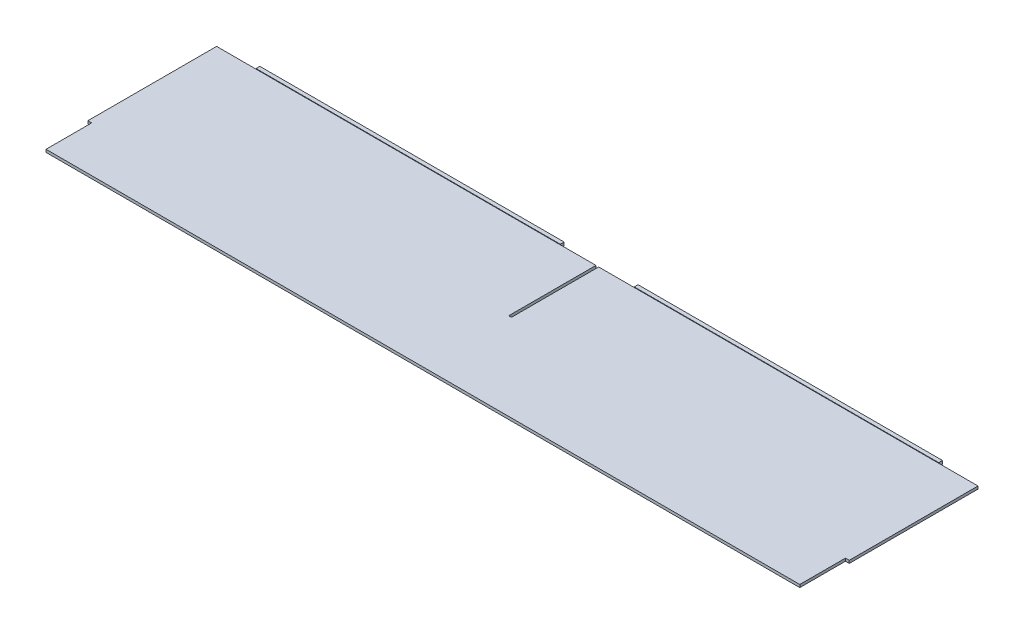
SolidWorks part; units mm, degrees
material "6061-T6 (SS)"
ref_plane "X-Y Datum" through (0, 0, 0) normal (0, 0, 1) x (1, 0, 0)
ref_plane "X-Z Datum" through (0, 0, 0) normal (0, 1, 0) x (1, 0, 0)
ref_plane "Y-Z Datum" through (0, 0, 0) normal (1, 0, 0) x (0, 0, -1)
sketch "Sketch1" plane through (0, 0, 0) normal (0, 1, 0) x (1, 0, 0)
  line L1 (-317.6778, 72.771) -> (317.6778, 72.771)
  line L2 (-317.6778, 72.771) -> (-317.6778, -72.771)
  line L3 (-317.6778, -72.771) -> (317.6778, -72.771)
  line L4 (317.6778, 72.771) -> (317.6778, -72.771)
  line L5 (-317.6778, 72.771) -> (317.6778, -72.771) construction
  line L6 (-317.6778, -72.771) -> (317.6778, 72.771) construction
  point P0 (0, 0)
  dimension "D1" = 635.3556
  dimension "D2" = 145.542
extrude "Boss-Extrude1" add sketch "Sketch1" along normal mid plane 2.286
sketch "Sketch2" plane through (0, 0, -72.771) normal (0, 0, -1) x (-1, 0, 0)
  line L20 (-317.6778, -1.143) -> (317.6778, -1.143) construction
  line L21 (-284.8229, -1.143) -> (-30.8229, -1.143)
  line L22 (30.8229, -1.143) -> (284.8229, -1.143)
  line L40 (30.8229, -1.143) -> (30.8229, 1.5875)
  line L41 (30.8229, 1.5875) -> (284.8229, 1.5875)
  line L42 (284.8229, 1.5875) -> (284.8229, -1.143)
  line L56 (-284.8229, -1.143) -> (-284.8229, 1.5875)
  line L57 (-284.8229, 1.5875) -> (-30.8229, 1.5875)
  line L58 (-30.8229, 1.5875) -> (-30.8229, -1.143)
extrude "Boss-Extrude2" add sketch "Sketch2" along normal blind 3.175
sketch "Sketch3" plane through (0, -1.143, 0) normal (0, -1, 0) x (1, 0, 0)
  line L1 (-317.6778, 72.771) -> (-314.5028, 72.771)
  line L2 (-317.6778, 72.771) -> (-317.6778, 34.671)
  line L3 (-317.6778, 34.671) -> (-314.5028, 34.671)
  line L4 (-314.5028, 72.771) -> (-314.5028, 34.671)
  dimension "D1" = 38.1
  dimension "D2" = 3.175
extrude "Cut-Extrude1" cut sketch "Sketch3" against normal through all
mirror "Mirror1" about plane through (0, 0, 0) normal (1, 0, 0) of "Cut-Extrude1"
sketch "Sketch4" plane through (0, -1.143, 0) normal (0, -1, 0) x (1, 0, 0)
  line L0 (30.8229, -72.771) -> (-30.8229, -72.771) construction
  line L1 (-1.143, -72.771) -> (1.143, -72.771)
  line L2 (-1.143, -72.771) -> (-1.143, 0)
  line L3 (-1.143, 0) -> (1.143, 0)
  line L4 (1.143, -72.771) -> (1.143, 0)
  line L5 (-1.143, -75.946) -> (-1.143, -72.771) construction
  dimension "D1" = 2.286
  dimension "D2" = 72.771
extrude "Cut-Extrude2" cut sketch "Sketch4" against normal through all
